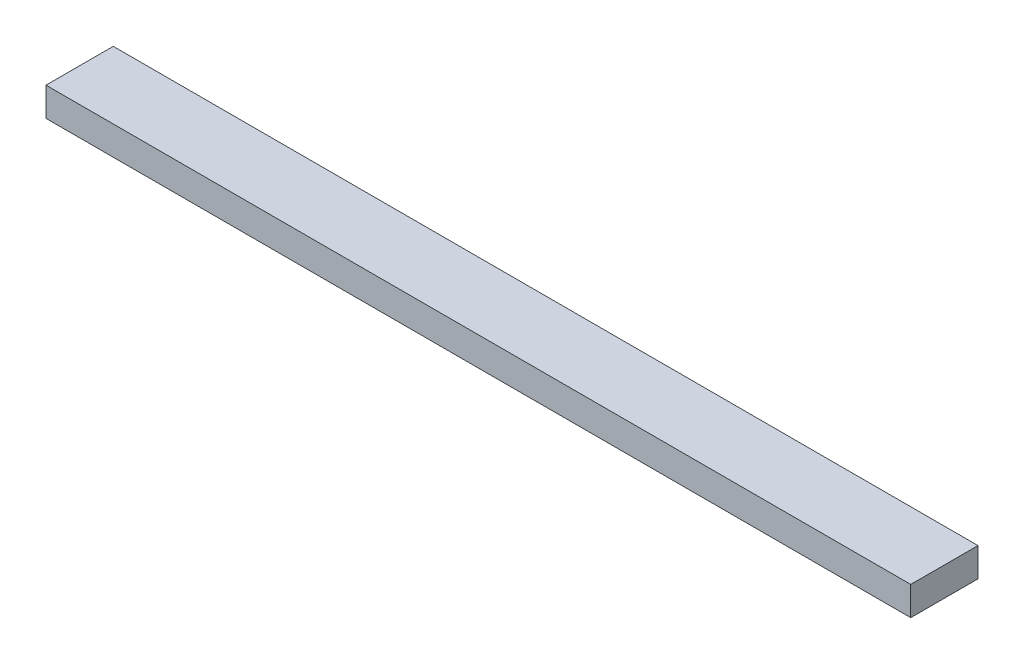
SolidWorks part; units mm, degrees
material "Pine"
ref_plane "Front Plane" through (0, 0, 0) normal (0, 0, 1) x (1, 0, 0)
ref_plane "Top Plane" through (0, 0, 0) normal (0, 1, 0) x (1, 0, 0)
ref_plane "Right Plane" through (0, 0, 0) normal (1, 0, 0) x (0, 0, -1)
sketch "Sketch1" plane through (0, 0, 0) normal (0, 1, 0) x (1, 0, 0)
  line L1 (0, 0) -> (1143, 0)
  line L2 (0, 0) -> (0, 88.9)
  line L3 (0, 88.9) -> (1143, 88.9)
  line L4 (1143, 0) -> (1143, 88.9)
  dimension "D1" = 88.9
  dimension "D2" = 1143
extrude "Boss-Extrude1" add sketch "Sketch1" along normal blind 38.1
